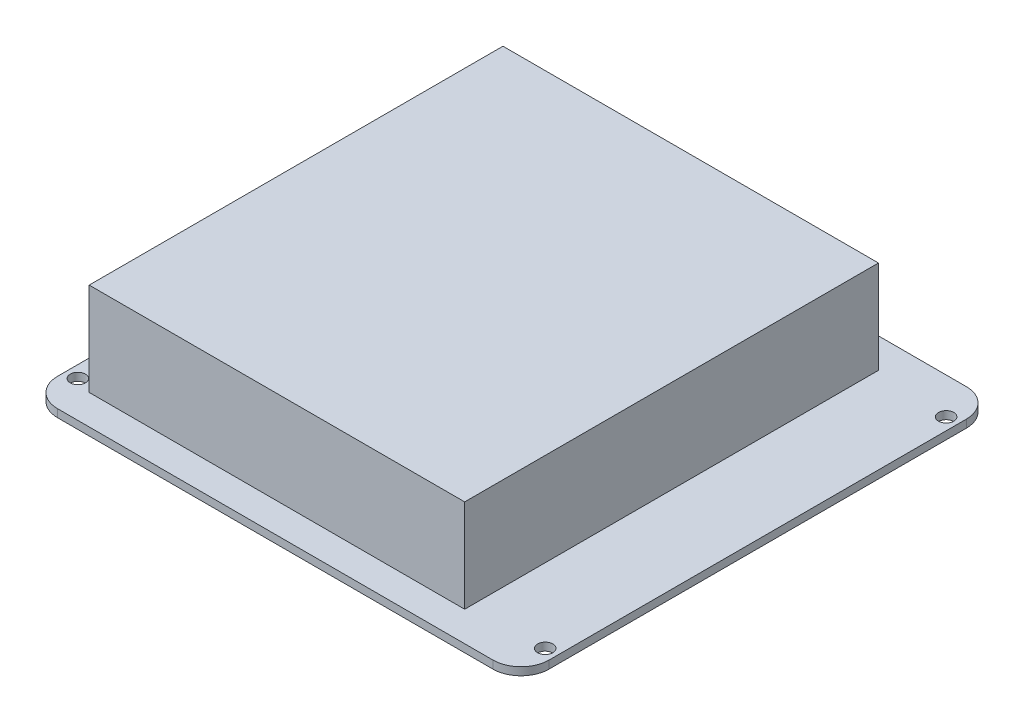
SolidWorks part; units mm, degrees
ref_plane "Front Plane" through (0, 0, 0) normal (0, 0, 1) x (1, 0, 0)
ref_plane "Top Plane" through (0, 0, 0) normal (0, 1, 0) x (1, 0, 0)
ref_plane "Right Plane" through (0, 0, 0) normal (1, 0, 0) x (0, 0, -1)
sketch "Sketch1" plane through (0, 0, 0) normal (0, 1, 0) x (1, 0, 0)
  line L0 (47.5, 40.75) -> (-47.5, 40.75) construction
  line L1 (-49.955, 48.125) -> (49.955, 48.125)
  line L2 (-49.955, 48.125) -> (-49.955, -48.125)
  line L3 (-49.955, -48.125) -> (49.955, -48.125)
  line L4 (49.955, 48.125) -> (49.955, -48.125)
  line L5 (47.5, -40.75) -> (47.5, 40.75) construction
  circle A0 centre (-47.5, 40.75) radius 1.55
  circle A1 centre (47.5, 40.75) radius 1.55
  circle A2 centre (-47.5, -40.75) radius 1.55
  circle A3 centre (47.5, -40.75) radius 1.55
  point P6 (0, 48.125)
  point P8 (49.955, 0)
  point P15 (0, 40.75)
  point P16 (47.5, 0)
  dimension "D3" = 3.1
  dimension "D1" = 96.25
  dimension "D2" = 99.91
  dimension "D4" = 95
  dimension "D5" = 81.5
extrude "Boss-Extrude1" add sketch "Sketch1" along normal blind 1.6
fillet "Fillet1" radius 5.7 4 edges at (49.955, 0.8, -48.125) (49.955, 0.8, 48.125) (-49.955, 0.8, -48.125) (-49.955, 0.8, 48.125)
sketch "Sketch2" plane through (0, 1.6, 0) normal (0, 1, 0) x (1, 0, 0)
  line L0 (-49.955, 42.425) -> (-49.955, -42.425) construction
  line L1 (32.435, -42.055) -> (-43.895, -42.055)
  line L2 (32.435, -42.055) -> (32.435, 42.055)
  line L3 (32.435, 42.055) -> (-43.895, 42.055)
  line L4 (-43.895, -42.055) -> (-43.895, 42.055)
  point P4 (-43.895, 0)
  dimension "D1" = 84.11
  dimension "D2" = 76.33
  dimension "D3" = 6.06
extrude "Boss-Extrude2" add sketch "Sketch2" along normal offset from surface (18.9 mm away) 20.5 up to face at (0, 0, 0)
sketch "Sketch3" plane through (0, 0, 0) normal (0, -1, 0) x (1, 0, 0)
  line L0 (-44.255, 48.125) -> (44.255, 48.125) construction
  line L1 (-7.135, 6.225) -> (-14.095, 6.225)
  line L2 (-7.135, 6.225) -> (-7.135, -0.325)
  line L3 (-7.135, -0.325) -> (-14.095, -0.325)
  line L4 (-14.095, 6.225) -> (-14.095, -0.325)
  line L5 (-49.955, -42.425) -> (-49.955, 42.425) construction
  dimension "D1" = 6.55
  dimension "D2" = 6.96
  dimension "D3" = 41.9
  dimension "D4" = 35.86
extrude "Boss-Extrude3" add sketch "Sketch3" along normal blind 5.15
